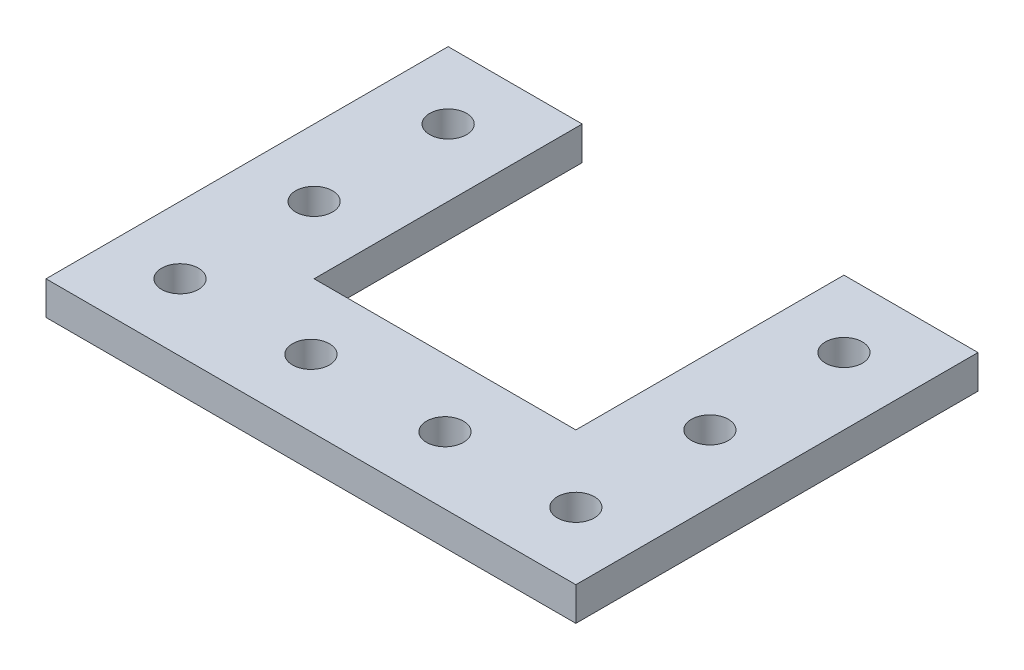
SolidWorks part; units mm, degrees
ref_plane "Front Plane" through (0, 0, 0) normal (0, 0, 1) x (1, 0, 0)
ref_plane "Top Plane" through (0, 0, 0) normal (0, 1, 0) x (1, 0, 0)
ref_plane "Right Plane" through (0, 0, 0) normal (1, 0, 0) x (0, 0, -1)
sketch "Sketch1" plane through (0, 0, 0) normal (0, 1, 0) x (1, 0, 0)
  line L0 (50.2, 0) -> (50.2, 114.9214) construction
  line L1 (0, 0) -> (100.4, 0)
  line L3 (25.4, 25.4) -> (75, 25.4)
  line L5 (100.4, 0) -> (75, 0)
  line L7 (100.4, 76.2) -> (75, 76.2)
  line L8 (75, 25.4) -> (75, 76.2)
  line L9 (25.4, 25.4) -> (25.4, 76.2)
  line L10 (0, 76.2) -> (25.4, 76.2)
  line L12 (0, 0) -> (25.4, 0)
  line L14 (0, 76.2) -> (0, -1.401)
  line L15 (100.4, 0) -> (100.4, 76.2)
  point P1 (50.2, 25.4)
  dimension "D1" = 100.4
  dimension "D2" = 76.2
  dimension "D3" = 25.4
  dimension "D4" = 25.4
extrude "Boss-Extrude1" add sketch "Sketch1" along normal blind 6.35 contours L0 L1 L15 L7 L8 L3 | L1 L0 L3 L9 L10 L14
sketch "Sketch2" plane through (0, 6.35, 0) normal (0, 1, 0) x (1, 0, 0)
  line L0 (12.7, 76.2) -> (12.7, 0) construction
  line L1 (0, 76.2) -> (25.4, 76.2) construction
  line L2 (0, 0) -> (100.4, 0) construction
  line L3 (50.2, 25.4) -> (50.2, 0) construction
  line L4 (25.4, 25.4) -> (75, 25.4) construction
  line L5 (12.7, 12.7) -> (87.7, 12.7) construction
  circle A0 centre (12.7, 12.7) radius 3.5
  circle A1 centre (12.7, 38.1) radius 3.5
  circle A2 centre (12.7, 63.5) radius 3.5
  circle A3 centre (87.7, 63.5) radius 3.5
  circle A4 centre (87.7, 38.1) radius 3.5
  circle A5 centre (87.7, 12.7) radius 3.5
  circle A6 centre (37.5, 12.7) radius 3.5
  circle A7 centre (62.9, 12.7) radius 3.5
  dimension "D1" = 7
  dimension "D2" = 12.7
  dimension "D4" = 12.7
  dimension "D5" = 12.7
  dimension "D3" = 3
extrude "Cut-Extrude1" cut sketch "Sketch2" against normal blind 6.35
